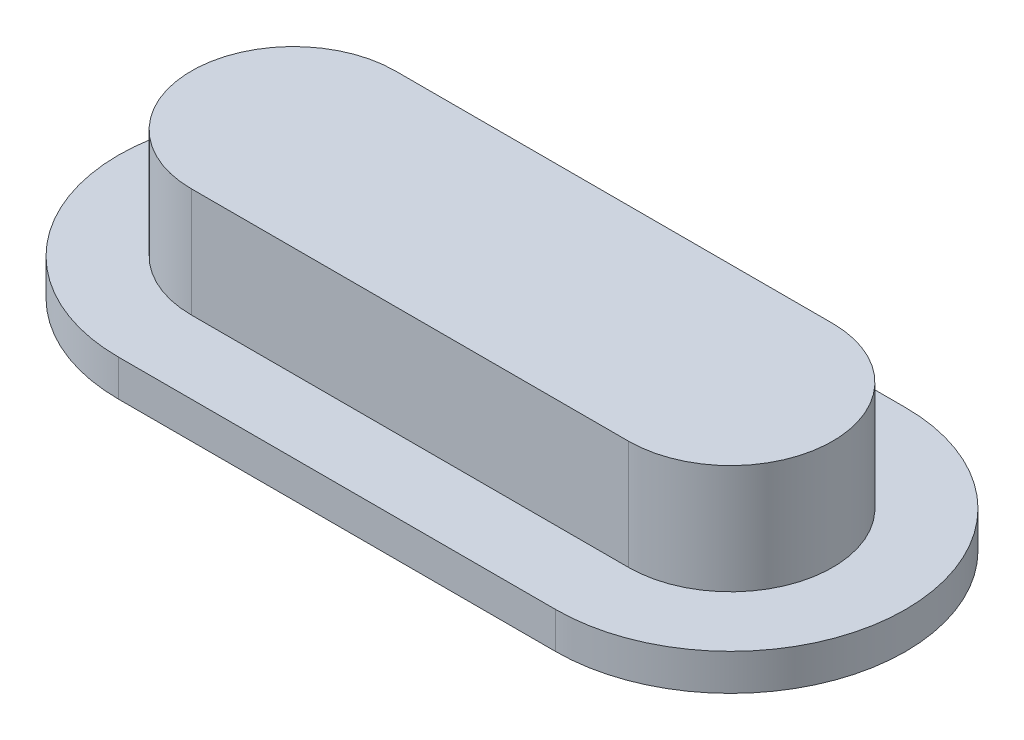
SolidWorks part; units mm, degrees
ref_plane "前视基准面" through (0, 0, 0) normal (0, 0, 1) x (1, 0, 0)
ref_plane "上视基准面" through (0, 0, 0) normal (0, 1, 0) x (1, 0, 0)
ref_plane "右视基准面" through (0, 0, 0) normal (1, 0, 0) x (0, 0, -1)
sketch "草图1" plane through (0, 0, 0) normal (0, 1, 0) x (1, 0, 0)
  line L0 (-3, 0) -> (3, 0) construction
  line L1 (-3, 1.4) -> (3, 1.4)
  line L2 (-3, -1.4) -> (3, -1.4)
  arc A0 (-3, 1.4) -> (-3, -1.4) centre (-3, 0) ccw
  arc A1 (3, -1.4) -> (3, 1.4) centre (3, 0) ccw
  point P2 (0, 0)
extrude "凸台-拉伸1" add sketch "草图1" along normal blind 1.5
sketch "草图2" plane through (0, 0, 0) normal (0, -1, 0) x (1, 0, 0)
  line L4 (-3, -2.4) -> (3, -2.4)
  line L5 (3, 2.4) -> (-3, 2.4)
  line L6 (-3, -2.4) -> (3, -2.4)
  line L7 (3, 2.4) -> (-3, 2.4)
  arc A4 (-3, 2.4) -> (-3, -2.4) centre (-3, 0) ccw
  arc A5 (3, -2.4) -> (3, 2.4) centre (3, 0) ccw
  arc A6 (-3, 2.4) -> (-3, -2.4) centre (-3, 0) ccw
  arc A7 (3, -2.4) -> (3, 2.4) centre (3, 0) ccw
  dimension "D1" = 1
extrude "凸台-拉伸2" add sketch "草图2" along normal blind 0.5
